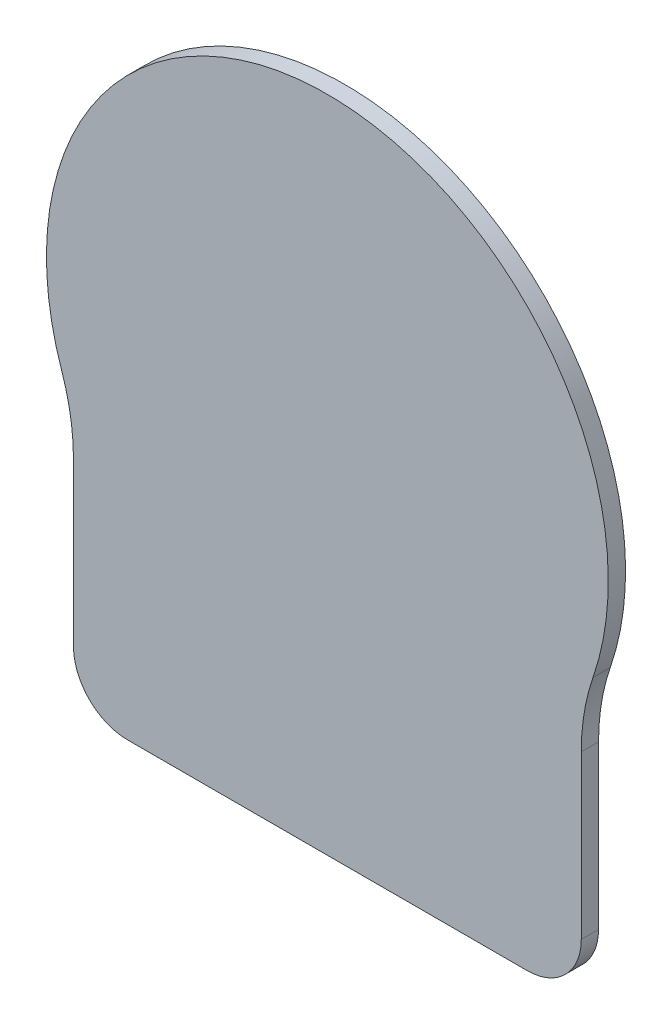
SolidWorks part; units mm, degrees
ref_plane "Front Plane" through (0, 0, 0) normal (0, 0, 1) x (1, 0, 0)
ref_plane "Top Plane" through (0, 0, 0) normal (0, 1, 0) x (1, 0, 0)
ref_plane "Right Plane" through (0, 0, 0) normal (1, 0, 0) x (0, 0, -1)
sketch "Sketch1" plane through (0, 0, 0) normal (0, 0, 1) x (1, 0, 0)
  line L0 (-23.5, 0) -> (-23.5, -11.1243) construction
  line L1 (-23.5, 0) -> (23.5, 0) construction
  line L2 (-23.5, -14.9583) -> (-23.5, -30)
  line L3 (-18.5, -35) -> (18.5, -35)
  line L4 (23.5, -14.9583) -> (23.5, -30)
  line L5 (23.5, 0) -> (23.5, -11.1243) construction
  arc A0 (24.587, -8.4547) -> (-24.587, -8.4547) centre (0, 0) ccw
  arc A1 (-23.5, -14.9583) -> (-24.587, -8.4547) centre (-43.5, -14.9583) ccw
  arc A2 (24.587, -8.4547) -> (23.5, -14.9583) centre (43.5, -14.9583) ccw
  arc A3 (18.5, -35) -> (23.5, -30) centre (18.5, -30) ccw
  arc A4 (-23.5, -30) -> (-18.5, -35) centre (-18.5, -30) ccw
  point P16 (23.5, -35)
  point P19 (-23.5, -35)
  dimension "D1" = 52
  dimension "D4" = 20
  dimension "D5" = 5
  dimension "D2" = 47
  dimension "D3" = 35
extrude "Boss-Extrude1" add sketch "Sketch1" along normal blind 1.6
